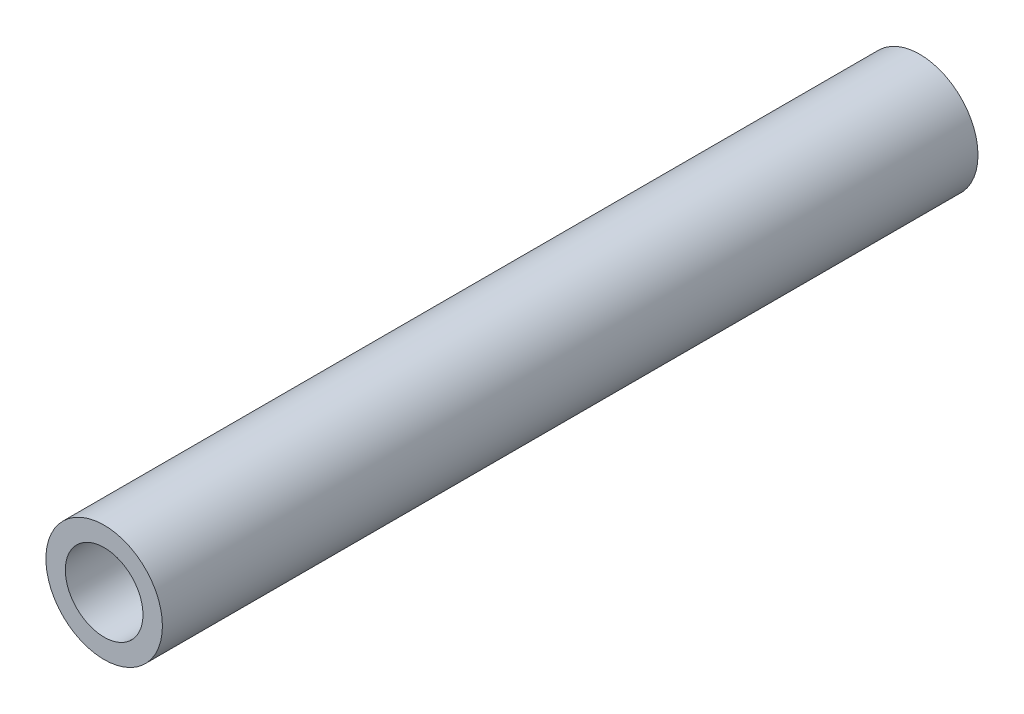
SolidWorks part; units mm, degrees
ref_plane "Alzado" through (0, 0, 0) normal (0, 0, 1) x (1, 0, 0)
ref_plane "Planta" through (0, 0, 0) normal (0, 1, 0) x (1, 0, 0)
ref_plane "Vista lateral" through (0, 0, 0) normal (1, 0, 0) x (0, 0, -1)
sketch "Croquis1" plane through (0, 0, 0) normal (0, 0, 1) x (1, 0, 0)
  circle A0 centre (0, 0) radius 1
  circle A1 centre (0, 0) radius 1.5
  dimension "D1" = 2
  dimension "D2" = 0.5
extrude "Saliente-Extruir1" add sketch "Croquis1" along normal blind 21
